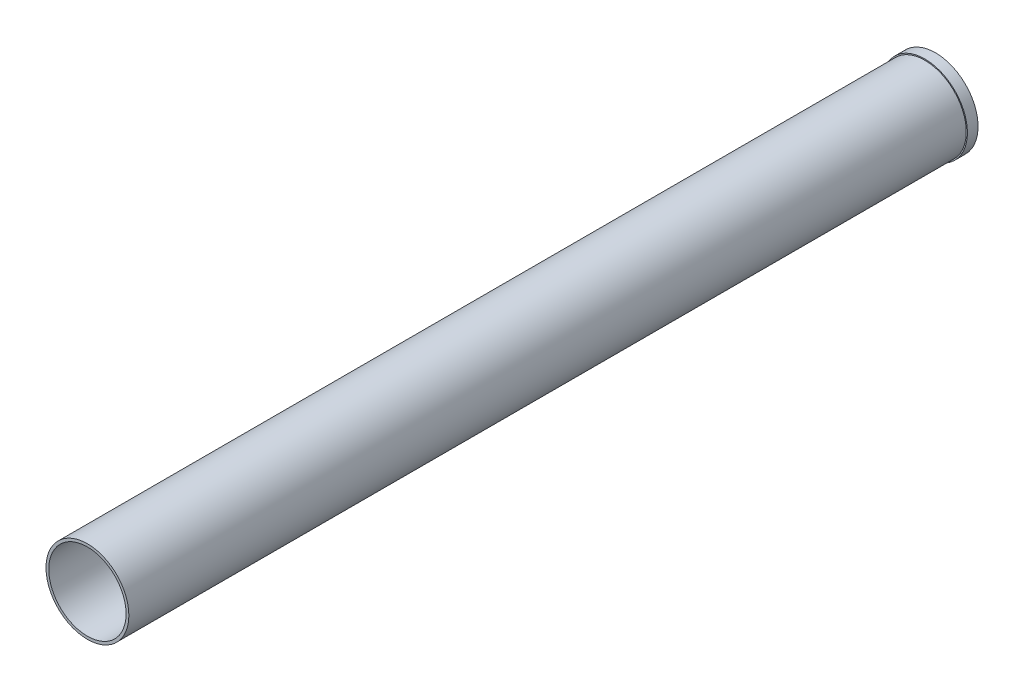
SolidWorks part; units mm, degrees
material "6061-T6 (SS)"
ref_plane "Front Plane" through (0, 0, 0) normal (0, 0, 1) x (1, 0, 0)
ref_plane "Top Plane" through (0, 0, 0) normal (0, 1, 0) x (1, 0, 0)
ref_plane "Right Plane" through (0, 0, 0) normal (1, 0, 0) x (0, 0, -1)
sketch "Sketch1" plane through (0, 0, 0) normal (0, 0, 1) x (1, 0, 0)
  circle A0 centre (0, 0) radius 49.3141
  circle A1 centre (0, 0) radius 46.0502
  dimension "D1" = 98.6282
  dimension "D2" = 92.1004
extrude "Boss-Extrude1" add sketch "Sketch1" along normal blind 1009.65
sketch "Sketch2" plane through (0, 0, 0) normal (0, 0, -1) x (-1, 0, 0)
  circle A0 centre (0, 0) radius 50.673
  circle A1 centre (0, 0) radius 49.3141
  dimension "D1" = 101.346
extrude "Boss-Extrude2" add sketch "Sketch2" against normal blind 12.7
